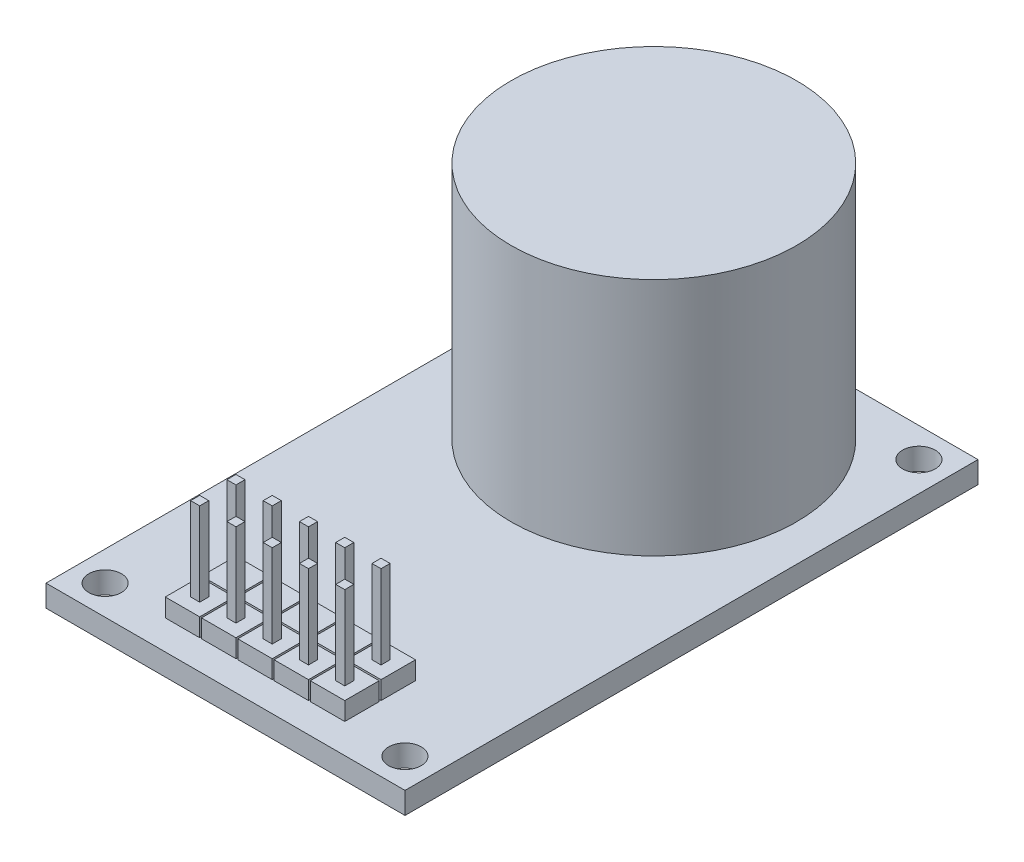
SolidWorks part; units mm, degrees
ref_plane "Front Plane" through (0, 0, 0) normal (0, 0, 1) x (1, 0, 0)
ref_plane "Top Plane" through (0, 0, 0) normal (0, 1, 0) x (1, 0, 0)
ref_plane "Right Plane" through (0, 0, 0) normal (1, 0, 0) x (0, 0, -1)
sketch "Sketch1" plane through (0, 0, 0) normal (0, 1, 0) x (1, 0, 0)
  line L0 (2.073, 38.066) -> (23.073, 38.066) construction
  line L1 (0, 40.132) -> (25.146, 40.132)
  line L2 (0, 40.132) -> (0, 0)
  line L3 (0, 0) -> (25.146, 0)
  line L4 (25.146, 40.132) -> (25.146, 0)
  line L5 (2.073, 2.066) -> (23.073, 2.066) construction
  line L6 (12.573, 38.066) -> (12.573, 2.066) construction
  line L7 (0, 20.066) -> (25.146, 20.066) construction
  circle A0 centre (2.073, 38.066) radius 1.143
  circle A1 centre (23.073, 38.066) radius 1.143
  circle A2 centre (23.073, 2.066) radius 1.143
  circle A3 centre (2.073, 2.066) radius 1.143
  point P13 (12.573, 20.066)
  dimension "D5" = 2.286
  dimension "D1" = 25.146
  dimension "D2" = 40.132
  dimension "D3" = 36
  dimension "D4" = 21
extrude "Boss-Extrude1" add sketch "Sketch1" along normal blind 1.524
sketch "Sketch2" plane through (0, 1.524, 0) normal (0, 1, 0) x (1, 0, 0)
  line L0 (12.573, 30) -> (12.573, 0) construction
  line L1 (0, 0) -> (25.146, 0) construction
  circle A0 centre (12.573, 30) radius 10
  dimension "D2" = 20
  dimension "D1" = 30
extrude "Boss-Extrude2" add sketch "Sketch2" along normal blind 16.764
sketch "Sketch3" plane through (0, 1.524, 0) normal (0, 1, 0) x (1, 0, 0)
  line L46 (6.2865, 4.479) -> (8.6995, 4.479)
  line L47 (6.2865, 4.479) -> (6.2865, 2.066)
  line L48 (6.2865, 2.066) -> (8.6995, 2.066)
  line L49 (8.6995, 4.479) -> (8.6995, 2.066)
  line L50 (8.8265, 4.479) -> (11.2395, 4.479)
  line L51 (8.8265, 4.479) -> (8.8265, 2.066)
  line L52 (8.8265, 2.066) -> (11.2395, 2.066)
  line L53 (11.2395, 4.479) -> (11.2395, 2.066)
  line L54 (11.3665, 4.479) -> (13.7795, 4.479)
  line L55 (11.3665, 4.479) -> (11.3665, 2.066)
  line L56 (11.3665, 2.066) -> (13.7795, 2.066)
  line L57 (13.7795, 4.479) -> (13.7795, 2.066)
  line L58 (13.9065, 4.479) -> (16.3195, 4.479)
  line L59 (13.9065, 4.479) -> (13.9065, 2.066)
  line L60 (13.9065, 2.066) -> (16.3195, 2.066)
  line L61 (16.3195, 4.479) -> (16.3195, 2.066)
  line L62 (16.4465, 4.479) -> (18.8595, 4.479)
  line L63 (16.4465, 4.479) -> (16.4465, 2.066)
  line L64 (16.4465, 2.066) -> (18.8595, 2.066)
  line L65 (18.8595, 4.479) -> (18.8595, 2.066)
  line L106 (6.2865, 7.019) -> (8.6995, 7.019)
  line L107 (6.2865, 7.019) -> (6.2865, 4.606)
  line L108 (6.2865, 4.606) -> (8.6995, 4.606)
  line L109 (8.6995, 7.019) -> (8.6995, 4.606)
  line L110 (8.8265, 7.019) -> (11.2395, 7.019)
  line L111 (8.8265, 7.019) -> (8.8265, 4.606)
  line L112 (8.8265, 4.606) -> (11.2395, 4.606)
  line L113 (11.2395, 7.019) -> (11.2395, 4.606)
  line L114 (11.3665, 7.019) -> (13.7795, 7.019)
  line L115 (11.3665, 7.019) -> (11.3665, 4.606)
  line L116 (11.3665, 4.606) -> (13.7795, 4.606)
  line L117 (13.7795, 7.019) -> (13.7795, 4.606)
  line L118 (13.9065, 7.019) -> (16.3195, 7.019)
  line L119 (13.9065, 7.019) -> (13.9065, 4.606)
  line L120 (13.9065, 4.606) -> (16.3195, 4.606)
  line L121 (16.3195, 7.019) -> (16.3195, 4.606)
  line L122 (16.4465, 7.019) -> (18.8595, 7.019)
  line L123 (16.4465, 7.019) -> (16.4465, 4.606)
  line L124 (16.4465, 4.606) -> (18.8595, 4.606)
  line L125 (18.8595, 7.019) -> (18.8595, 4.606)
  line L130 (2.073, 2.066) -> (23.073, 2.066) construction
  circle A0 centre (2.073, 2.066) radius 1.143 construction
  circle A1 centre (23.073, 2.066) radius 1.143 construction
  point P6 (12.573, 2.066)
  dimension "D1" = 0.127
  dimension "D2" = 2.413
extrude "Boss-Extrude3" add sketch "Sketch3" along normal blind 1.27
sketch "Sketch4" plane through (0, 2.794, 0) normal (0, 1, 0) x (1, 0, 0)
  line L0 (7.493, 4.479) -> (7.493, 2.066) construction
  line L1 (8.6995, 4.479) -> (6.2865, 4.479) construction
  line L2 (6.2865, 2.066) -> (8.6995, 2.066) construction
  line L3 (9.7155, 3.59) -> (10.3505, 3.59)
  line L4 (9.7155, 3.59) -> (9.7155, 2.955)
  line L5 (7.1755, 3.2725) -> (7.8105, 3.2725) construction
  line L7 (7.1755, 3.59) -> (7.8105, 3.59)
  line L8 (7.1755, 3.59) -> (7.1755, 2.955)
  line L9 (7.1755, 2.955) -> (7.8105, 2.955)
  line L10 (7.8105, 3.59) -> (7.8105, 2.955)
  line L134 (9.7155, 2.955) -> (10.3505, 2.955)
  line L135 (10.3505, 3.59) -> (10.3505, 2.955)
  line L136 (9.7155, 3.2725) -> (10.3505, 3.2725) construction
  line L137 (12.2555, 3.59) -> (12.8905, 3.59)
  line L138 (12.2555, 3.59) -> (12.2555, 2.955)
  line L139 (12.2555, 2.955) -> (12.8905, 2.955)
  line L140 (12.8905, 3.59) -> (12.8905, 2.955)
  line L141 (12.2555, 3.2725) -> (12.8905, 3.2725) construction
  line L142 (14.7955, 3.59) -> (15.4305, 3.59)
  line L143 (14.7955, 3.59) -> (14.7955, 2.955)
  line L144 (14.7955, 2.955) -> (15.4305, 2.955)
  line L145 (15.4305, 3.59) -> (15.4305, 2.955)
  line L146 (14.7955, 3.2725) -> (15.4305, 3.2725) construction
  line L147 (17.3355, 3.59) -> (17.9705, 3.59)
  line L148 (17.3355, 3.59) -> (17.3355, 2.955)
  line L149 (17.3355, 2.955) -> (17.9705, 2.955)
  line L150 (17.9705, 3.59) -> (17.9705, 2.955)
  line L151 (17.3355, 3.2725) -> (17.9705, 3.2725) construction
  line L152 (9.7155, 6.13) -> (10.3505, 6.13)
  line L153 (9.7155, 6.13) -> (9.7155, 5.495)
  line L154 (9.7155, 5.495) -> (10.3505, 5.495)
  line L155 (10.3505, 6.13) -> (10.3505, 5.495)
  line L156 (9.7155, 5.8125) -> (10.3505, 5.8125) construction
  line L157 (12.2555, 6.13) -> (12.8905, 6.13)
  line L158 (12.2555, 6.13) -> (12.2555, 5.495)
  line L159 (12.2555, 5.495) -> (12.8905, 5.495)
  line L160 (12.8905, 6.13) -> (12.8905, 5.495)
  line L161 (12.2555, 5.8125) -> (12.8905, 5.8125) construction
  line L162 (14.7955, 6.13) -> (15.4305, 6.13)
  line L163 (14.7955, 6.13) -> (14.7955, 5.495)
  line L164 (14.7955, 5.495) -> (15.4305, 5.495)
  line L165 (15.4305, 6.13) -> (15.4305, 5.495)
  line L166 (14.7955, 5.8125) -> (15.4305, 5.8125) construction
  line L167 (17.3355, 6.13) -> (17.9705, 6.13)
  line L168 (17.3355, 6.13) -> (17.3355, 5.495)
  line L169 (17.3355, 5.495) -> (17.9705, 5.495)
  line L170 (17.9705, 6.13) -> (17.9705, 5.495)
  line L171 (17.3355, 5.8125) -> (17.9705, 5.8125) construction
  line L172 (7.1755, 6.13) -> (7.8105, 6.13)
  line L173 (7.1755, 6.13) -> (7.1755, 5.495)
  line L174 (7.1755, 5.495) -> (7.8105, 5.495)
  line L175 (7.8105, 6.13) -> (7.8105, 5.495)
  line L176 (7.1755, 5.8125) -> (7.8105, 5.8125) construction
  point P8 (7.493, 3.2725)
  point P17 (10.033, 3.2725)
  point P24 (12.573, 3.2725)
  point P31 (15.113, 3.2725)
  point P38 (17.653, 3.2725)
  point P45 (10.033, 5.8125)
  point P52 (12.573, 5.8125)
  point P59 (15.113, 5.8125)
  point P66 (17.653, 5.8125)
  point P73 (7.493, 5.8125)
  dimension "D1" = 0.635
  dimension "D2" = 5
extrude "Boss-Extrude4" add sketch "Sketch4" along normal blind 5.842
sketch "Sketch5" plane through (0, 0, 0) normal (0, -1, 0) x (1, 0, 0)
  line L1 (4.8902, -32.0409) -> (1.5413, -32.0409)
  line L2 (4.8902, -32.0409) -> (4.8902, -26.3209)
  line L3 (4.8902, -26.3209) -> (1.5413, -26.3209)
  line L4 (1.5413, -32.0409) -> (1.5413, -26.3209)
extrude "Boss-Extrude5" add sketch "Sketch5" along normal blind 3.302
